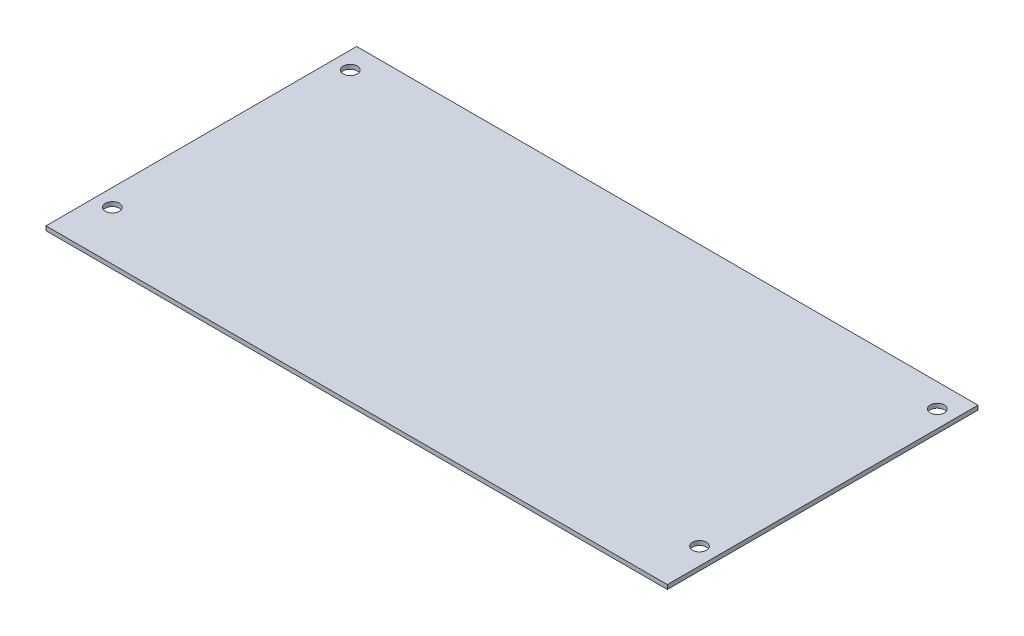
SolidWorks part; units mm, degrees
ref_plane "Front Plane" through (0, 0, 0) normal (0, 0, 1) x (1, 0, 0)
ref_plane "Top Plane" through (0, 0, 0) normal (0, 1, 0) x (1, 0, 0)
ref_plane "Right Plane" through (0, 0, 0) normal (1, 0, 0) x (0, 0, -1)
sketch "Sketch2" plane through (0, 0, 0) normal (0, 1, 0) x (1, 0, 0)
  line L1 (0, 0) -> (-290, 0)
  line L2 (0, 0) -> (0, 145)
  line L3 (0, 145) -> (-290, 145)
  line L4 (-290, 0) -> (-290, 145)
  circle A0 centre (-282, 134) radius 3.25
  circle A1 centre (-282, 23) radius 3.25
  circle A4 centre (-8, 23) radius 3.25
  circle A5 centre (-8, 134) radius 3.25
  dimension "D3" = 6.5
  dimension "D4" = 11
  dimension "D5" = 8
  dimension "D6" = 6.5
  dimension "D7" = 23
  dimension "D11" = 6.5
  dimension "D14" = 6.5
  dimension "D15" = 11
  dimension "D16" = 8
  dimension "D1" = 290
  dimension "D2" = 145
  dimension "D8" = 8
  dimension "D12" = 8
  dimension "D13" = 23
extrude "Boss-Extrude1" add sketch "Sketch2" along normal blind 2
